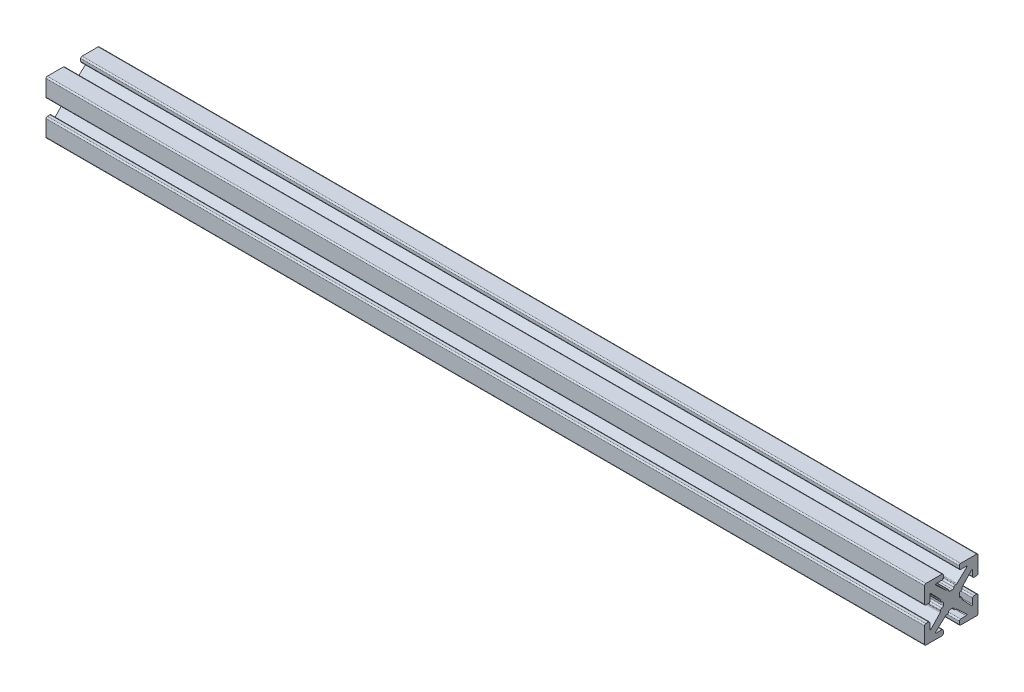
SolidWorks part; units mm, degrees
ref_plane "Front Plane" through (0, 0, 0) normal (0, 0, 1) x (1, 0, 0)
ref_plane "Top Plane" through (0, 0, 0) normal (0, 1, 0) x (1, 0, 0)
ref_plane "Right Plane" through (0, 0, 0) normal (1, 0, 0) x (0, 0, -1)
sketch "Sketch1" plane through (0, 0, 0) normal (1, 0, 0) x (0, 0, -1)
  line L0 (0, 0) -> (0, 1.4986) construction
  line L1 (-0.2413, 1.4986) -> (0.2413, 1.4986)
  line L2 (5.0038, 1.7526) -> (5.0038, 4.7498)
  line L3 (0.7493, 2.0066) -> (0.8899, 2.0066)
  line L4 (1.0639, 2.0756) -> (2.8908, 3.7937)
  line L5 (2.8038, 4.0132) -> (1.7526, 4.0132)
  line L6 (1.4986, 4.2672) -> (1.4986, 4.7498)
  line L7 (1.7526, 5.0038) -> (4.7498, 5.0038)
  line L8 (5.0038, 5.0038) -> (0, 0) construction
  line L9 (0, 0) -> (8.6271, 0) construction
  line L10 (0, 0) -> (0, 5.0038) construction
  line L11 (4.2672, 1.4986) -> (4.7498, 1.4986)
  line L12 (4.0132, 2.8038) -> (4.0132, 1.7526)
  line L13 (2.0756, 1.0639) -> (3.7937, 2.8908)
  line L14 (2.0066, 0.7493) -> (2.0066, 0.8899)
  line L15 (1.4986, -0.2413) -> (1.4986, 0.2413)
  line L16 (0, 0) -> (1.4986, 0) construction
  line L17 (-0.2413, -1.4986) -> (0.2413, -1.4986)
  line L18 (0.7493, -2.0066) -> (0.8899, -2.0066)
  line L19 (1.0639, -2.0756) -> (2.8908, -3.7937)
  line L20 (2.8038, -4.0132) -> (1.7526, -4.0132)
  line L21 (1.4986, -4.2672) -> (1.4986, -4.7498)
  line L22 (1.7526, -5.0038) -> (4.7498, -5.0038)
  line L23 (5.0038, -1.7526) -> (5.0038, -4.7498)
  line L24 (4.2672, -1.4986) -> (4.7498, -1.4986)
  line L25 (4.0132, -2.8038) -> (4.0132, -1.7526)
  line L26 (2.0756, -1.0639) -> (3.7937, -2.8908)
  line L27 (2.0066, -0.7493) -> (2.0066, -0.8899)
  line L28 (-0.7493, 2.0066) -> (-0.8899, 2.0066)
  line L29 (-1.0639, 2.0756) -> (-2.8908, 3.7937)
  line L30 (-2.8038, 4.0132) -> (-1.7526, 4.0132)
  line L31 (-1.4986, 4.2672) -> (-1.4986, 4.7498)
  line L32 (-1.7526, 5.0038) -> (-4.7498, 5.0038)
  line L33 (-5.0038, 1.7526) -> (-5.0038, 4.7498)
  line L34 (-4.2672, 1.4986) -> (-4.7498, 1.4986)
  line L35 (-4.0132, 2.8038) -> (-4.0132, 1.7526)
  line L36 (-2.0756, 1.0639) -> (-3.7937, 2.8908)
  line L37 (-2.0066, 0.7493) -> (-2.0066, 0.8899)
  line L38 (-1.4986, -0.2413) -> (-1.4986, 0.2413)
  line L39 (-2.0066, -0.7493) -> (-2.0066, -0.8899)
  line L40 (-2.0756, -1.0639) -> (-3.7937, -2.8908)
  line L41 (-4.0132, -2.8038) -> (-4.0132, -1.7526)
  line L42 (-4.2672, -1.4986) -> (-4.7498, -1.4986)
  line L43 (-5.0038, -1.7526) -> (-5.0038, -4.7498)
  line L44 (-1.7526, -5.0038) -> (-4.7498, -5.0038)
  line L45 (-1.4986, -4.2672) -> (-1.4986, -4.7498)
  line L46 (-2.8038, -4.0132) -> (-1.7526, -4.0132)
  line L47 (-1.0639, -2.0756) -> (-2.8908, -3.7937)
  line L48 (-0.7493, -2.0066) -> (-0.8899, -2.0066)
  arc A0 (2.8908, 3.7937) -> (2.8038, 4.0132) centre (2.8038, 3.8862) ccw
  arc A1 (0.4953, 1.7526) -> (0.7493, 2.0066) centre (0.7493, 1.7526) cw
  arc A2 (0.8899, 2.0066) -> (1.0639, 2.0756) centre (0.8899, 2.2606) ccw
  arc A3 (1.7526, 4.0132) -> (1.4986, 4.2672) centre (1.7526, 4.2672) cw
  arc A4 (1.4986, 4.7498) -> (1.7526, 5.0038) centre (1.7526, 4.7498) cw
  arc A5 (0.2413, 1.4986) -> (0.4953, 1.7526) centre (0.2413, 1.7526) ccw
  arc A6 (4.7498, 1.4986) -> (5.0038, 1.7526) centre (4.7498, 1.7526) ccw
  arc A7 (4.0132, 1.7526) -> (4.2672, 1.4986) centre (4.2672, 1.7526) ccw
  arc A8 (3.7937, 2.8908) -> (4.0132, 2.8038) centre (3.8862, 2.8038) cw
  arc A9 (2.0066, 0.8899) -> (2.0756, 1.0639) centre (2.2606, 0.8899) cw
  arc A10 (1.7526, 0.4953) -> (2.0066, 0.7493) centre (1.7526, 0.7493) ccw
  arc A11 (1.4986, 0.2413) -> (1.7526, 0.4953) centre (1.7526, 0.2413) cw
  arc A12 (0.2413, -1.4986) -> (0.4953, -1.7526) centre (0.2413, -1.7526) cw
  arc A13 (0.4953, -1.7526) -> (0.7493, -2.0066) centre (0.7493, -1.7526) ccw
  arc A14 (0.8899, -2.0066) -> (1.0639, -2.0756) centre (0.8899, -2.2606) cw
  arc A15 (2.8908, -3.7937) -> (2.8038, -4.0132) centre (2.8038, -3.8862) cw
  arc A16 (1.7526, -4.0132) -> (1.4986, -4.2672) centre (1.7526, -4.2672) ccw
  arc A17 (1.4986, -4.7498) -> (1.7526, -5.0038) centre (1.7526, -4.7498) ccw
  arc A18 (4.7498, -1.4986) -> (5.0038, -1.7526) centre (4.7498, -1.7526) cw
  arc A19 (4.0132, -1.7526) -> (4.2672, -1.4986) centre (4.2672, -1.7526) cw
  arc A20 (3.7937, -2.8908) -> (4.0132, -2.8038) centre (3.8862, -2.8038) ccw
  arc A21 (2.0066, -0.8899) -> (2.0756, -1.0639) centre (2.2606, -0.8899) ccw
  arc A22 (1.7526, -0.4953) -> (2.0066, -0.7493) centre (1.7526, -0.7493) cw
  arc A23 (1.4986, -0.2413) -> (1.7526, -0.4953) centre (1.7526, -0.2413) ccw
  arc A24 (-0.2413, 1.4986) -> (-0.4953, 1.7526) centre (-0.2413, 1.7526) cw
  arc A25 (-0.4953, 1.7526) -> (-0.7493, 2.0066) centre (-0.7493, 1.7526) ccw
  arc A26 (-0.8899, 2.0066) -> (-1.0639, 2.0756) centre (-0.8899, 2.2606) cw
  arc A27 (-2.8908, 3.7937) -> (-2.8038, 4.0132) centre (-2.8038, 3.8862) cw
  arc A28 (-1.7526, 4.0132) -> (-1.4986, 4.2672) centre (-1.7526, 4.2672) ccw
  arc A29 (-1.4986, 4.7498) -> (-1.7526, 5.0038) centre (-1.7526, 4.7498) ccw
  arc A30 (-4.7498, 1.4986) -> (-5.0038, 1.7526) centre (-4.7498, 1.7526) cw
  arc A31 (-4.0132, 1.7526) -> (-4.2672, 1.4986) centre (-4.2672, 1.7526) cw
  arc A32 (-3.7937, 2.8908) -> (-4.0132, 2.8038) centre (-3.8862, 2.8038) ccw
  arc A33 (-2.0066, 0.8899) -> (-2.0756, 1.0639) centre (-2.2606, 0.8899) ccw
  arc A34 (-1.7526, 0.4953) -> (-2.0066, 0.7493) centre (-1.7526, 0.7493) cw
  arc A35 (-1.4986, 0.2413) -> (-1.7526, 0.4953) centre (-1.7526, 0.2413) ccw
  arc A36 (-1.4986, -0.2413) -> (-1.7526, -0.4953) centre (-1.7526, -0.2413) cw
  arc A37 (-1.7526, -0.4953) -> (-2.0066, -0.7493) centre (-1.7526, -0.7493) ccw
  arc A38 (-2.0066, -0.8899) -> (-2.0756, -1.0639) centre (-2.2606, -0.8899) cw
  arc A39 (-3.7937, -2.8908) -> (-4.0132, -2.8038) centre (-3.8862, -2.8038) cw
  arc A40 (-4.0132, -1.7526) -> (-4.2672, -1.4986) centre (-4.2672, -1.7526) ccw
  arc A41 (-4.7498, -1.4986) -> (-5.0038, -1.7526) centre (-4.7498, -1.7526) ccw
  arc A42 (-1.4986, -4.7498) -> (-1.7526, -5.0038) centre (-1.7526, -4.7498) cw
  arc A43 (-1.7526, -4.0132) -> (-1.4986, -4.2672) centre (-1.7526, -4.2672) cw
  arc A44 (-2.8908, -3.7937) -> (-2.8038, -4.0132) centre (-2.8038, -3.8862) ccw
  arc A45 (-0.8899, -2.0066) -> (-1.0639, -2.0756) centre (-0.8899, -2.2606) ccw
  arc A46 (-0.4953, -1.7526) -> (-0.7493, -2.0066) centre (-0.7493, -1.7526) cw
  arc A47 (-0.2413, -1.4986) -> (-0.4953, -1.7526) centre (-0.2413, -1.7526) ccw
  arc A48 (-4.7498, 5.0038) -> (-5.0038, 4.7498) centre (-4.7498, 4.7498) ccw
  arc A49 (-5.0038, -4.7498) -> (-4.7498, -5.0038) centre (-4.7498, -4.7498) ccw
  arc A50 (4.7498, -5.0038) -> (5.0038, -4.7498) centre (4.7498, -4.7498) ccw
  arc A51 (4.7498, 5.0038) -> (5.0038, 4.7498) centre (4.7498, 4.7498) cw
  point P14 (3.1242, 4.0132)
  point P19 (0.9906, 2.0066)
  point P150 (0, -1.4986)
  point P152 (-5.0038, 5.0038)
  point P155 (-5.0038, -5.0038)
  point P158 (5.0038, -5.0038)
  dimension "D10" = 0.127
  dimension "D11" = 0.254
  dimension "D2" = 0.254
  dimension "D1" = 10.0076
  dimension "D3" = 2.9972
  dimension "D4" = 0.508
  dimension "D5" = 2.9972
  dimension "D6" = 0.9906
  dimension "D7" = 1.6256
  dimension "D8" = 1.9812
  dimension "D9" = 0.9906
extrude "Boss.-Extru.1" add sketch "Sketch1" along normal blind 164.48
